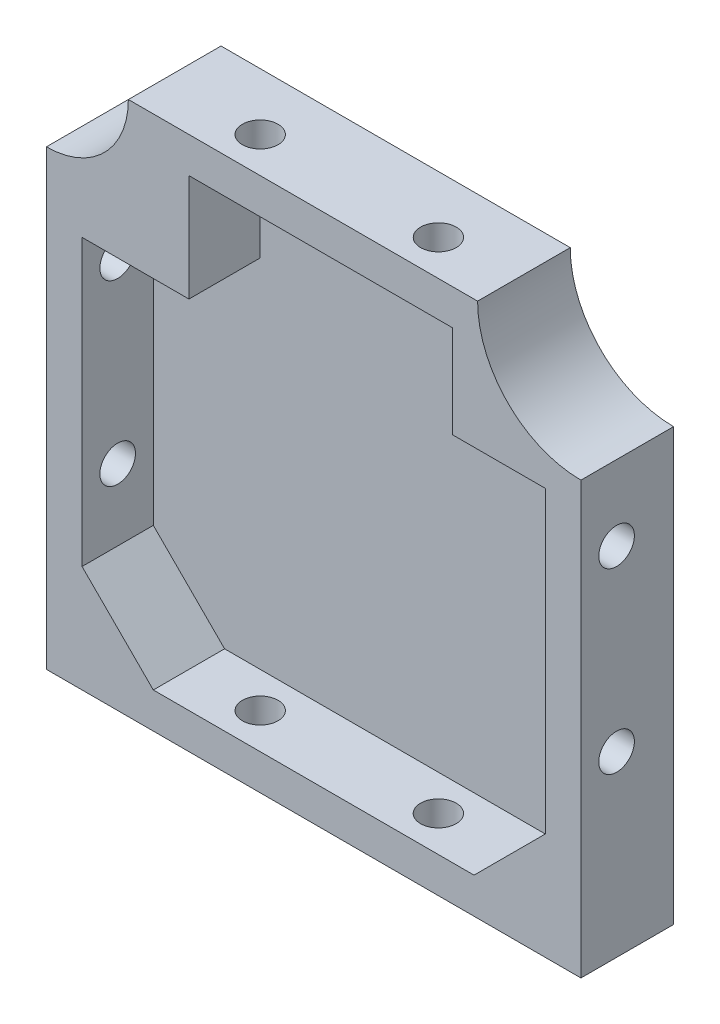
SolidWorks part; units mm, degrees
ref_plane "Plan de face" through (0, 0, 0) normal (0, 0, 1) x (1, 0, 0)
ref_plane "Plan de dessus" through (0, 0, 0) normal (0, 1, 0) x (1, 0, 0)
ref_plane "Plan de droite" through (0, 0, 0) normal (1, 0, 0) x (0, 0, -1)
sketch "Esquisse1" plane through (0, 0, 0) normal (0, 0, 1) x (1, 0, 0)
  line L0 (44.1184, 33.7284) -> (54.1184, 33.7284)
  line L1 (-20.8816, 33.7284) -> (44.1184, 33.7284)
  line L2 (-20.8816, 33.7284) -> (-20.8816, -41.2716)
  line L3 (-20.8816, -41.2716) -> (54.1184, -41.2716)
  line L4 (54.1184, 23.7284) -> (54.1184, -41.2716)
  line L5 (54.1184, 33.7284) -> (54.1184, 23.7284)
  point P6 (54.1184, 33.7284)
  dimension "D1" = 75
  dimension "D2" = 75
extrude "Boss.-Extru.1" add sketch "Esquisse1" along normal blind 13
shell "Coque1" thickness 5
sketch "Esquisse2" plane through (-20.8816, 0, 0) normal (-1, 0, 0) x (0, 0, 1)
  line L0 (13, 33.7284) -> (13, -41.2716) construction
  line L1 (13, 33.7284) -> (0, 33.7284) construction
  line L2 (13, -41.2716) -> (0, -41.2716) construction
  circle A0 centre (8, 8.7284) radius 2.5
  circle A1 centre (8, -16.2716) radius 2.5
  dimension "D1" = 5
  dimension "D2" = 5
  dimension "D3" = 5
  dimension "D4" = 5
  dimension "D5" = 25
  dimension "D6" = 25
extrude "Enlèv. mat.-Extru.1" cut sketch "Esquisse2" against normal up to surface (75 mm away) contours A1 | A0 up to face at (54.1184, -3.7716, 6.5)
sketch "Esquisse3" plane through (0, -41.2716, 0) normal (0, -1, 0) x (1, 0, 0)
  line L0 (-20.8816, 13) -> (54.1184, 13) construction
  line L2 (54.1184, 13) -> (54.1184, 0) construction
  line L3 (-20.8816, 13) -> (-20.8816, 0) construction
  circle A0 centre (4.1184, 8) radius 2.5
  circle A1 centre (29.1184, 8) radius 2.5
  dimension "D1" = 5
  dimension "D2" = 5
  dimension "D3" = 5
  dimension "D4" = 5
  dimension "D5" = 25
  dimension "D6" = 25
extrude "Enlèv. mat.-Extru.2" cut sketch "Esquisse3" against normal up to surface (75 mm away) up to face at (16.6184, 33.7284, 6.5)
sketch "Esquisse4" plane through (0, 0, 3) normal (0, 0, 1) x (1, 0, 0)
  line L0 (-15.8816, -26.2716) -> (-5.8816, -36.2716)
  line L3 (-15.8816, 28.7284) -> (-15.8816, -36.2716) construction
  line L4 (-5.8816, -36.2716) -> (-15.8816, -36.2716)
  line L5 (54.1184, 33.7284) -> (36.1184, 33.7284)
  line L6 (49.1184, -36.2716) -> (49.1184, 28.7284) construction
  line L7 (54.1184, 33.7284) -> (54.1184, 15.7284)
  line L8 (54.1184, 15.7284) -> (36.1184, 15.7284)
  line L10 (49.1184, -36.2716) -> (49.1184, -26.2716)
  line L11 (49.1184, -26.2716) -> (39.1184, -36.2716)
  line L12 (-15.8816, -36.2716) -> (49.1184, -36.2716) construction
  line L13 (39.1184, -36.2716) -> (49.1184, -36.2716)
  line L14 (-15.8816, -36.2716) -> (-15.8816, -26.2716)
  line L15 (36.1184, 33.7284) -> (36.1184, 15.7284)
  line L16 (-15.8816, 28.7284) -> (-0.8816, 28.7284)
  line L17 (-15.8816, 28.7284) -> (-15.8816, 13.7284)
  line L18 (-15.8816, 13.7284) -> (-0.8816, 13.7284)
  line L19 (-0.8816, 28.7284) -> (-0.8816, 13.7284)
  dimension "D1" = 10
  dimension "D2" = 10
  dimension "D3" = 18
  dimension "D4" = 18
  dimension "D5" = 10
  dimension "D6" = 10
  dimension "D7" = 15
  dimension "D8" = 15
extrude "Boss.-Extru.2" add sketch "Esquisse4" along normal up to surface (10 mm away) up to face at (16.6184, -3.7716, 13)
sketch "Esquisse5" plane through (0, 0, 13) normal (0, 0, 1) x (1, 0, 0)
  line L0 (54.1184, 33.7284) -> (-20.8816, 33.7284) construction
  line L1 (-20.8816, 33.7284) -> (-20.8816, -41.2716) construction
  circle A0 centre (-20.8816, 33.7284) radius 11.5
  circle A1 centre (54.1184, 33.7284) radius 14.5
  dimension "D1" = 23
  dimension "D2" = 29
extrude "Enlèv. mat.-Extru.3" cut sketch "Esquisse5" against normal up to surface (13 mm away) up to face at (16.6184, -3.7716, 0)
